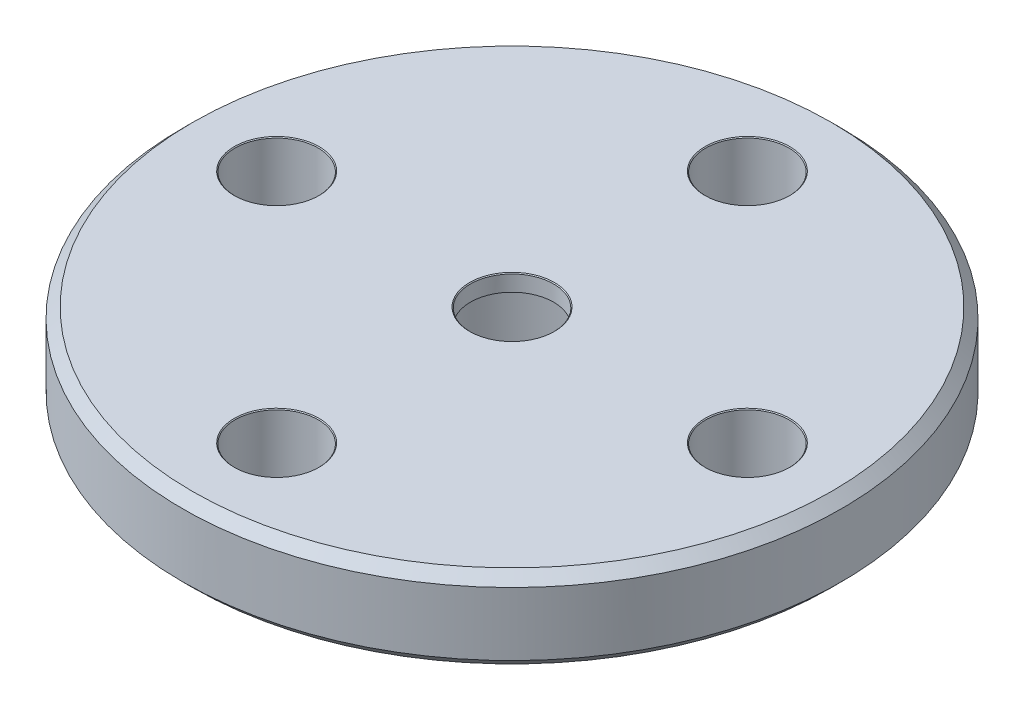
SolidWorks part; units mm, degrees
ref_plane "前视基准面" through (0, 0, 0) normal (0, 0, 1) x (1, 0, 0)
ref_plane "上视基准面" through (0, 0, 0) normal (0, 1, 0) x (1, 0, 0)
ref_plane "右视基准面" through (0, 0, 0) normal (1, 0, 0) x (0, 0, -1)
other "Configuration Table"
sketch "草图2" plane through (0, 0, 0) normal (0, 0, 1) x (1, 0, 0)
  line L0 (0, 0) -> (0, 4.6)
  line L1 (0, 4.6) -> (9.9, 4.6)
  line L2 (9.9, 4.6) -> (9.9, 2.1)
  line L3 (9.9, 2.1) -> (4.95, 2.1)
  line L4 (4.95, 2.1) -> (4.95, 0)
  line L5 (4.95, 0) -> (0, 0)
  dimension "D1" = 9.9
  dimension "D2" = 2.1
  dimension "D3" = 2.5
  dimension "D4" = 4.95
revolve "旋转1" add sketch "草图2" angle 360 about L0
chamfer "倒角1" distance 0.3 angle 45 3 edges at (0, 0, -4.95) (0, 2.1, -9.9) (0, 4.6, -9.9)
sketch "草图3" plane through (0, 4.6, 0) normal (0, 1, 0) x (1, 0, 0)
  line L0 (0, 0) -> (14.3811, 0) construction
  point P0 (7.0711, 0)
  point P4 (0, -7.0711)
  point P5 (-7.0711, 0)
  point P6 (0, 7.0711)
  point P7 (0, 0)
  dimension "D2" = 10
  dimension "D1" = 4
hole_wizard "M3 螺纹孔的螺纹孔钻头1" positions "草图3" profile "草图4" hole size "M3" standard "GB" end condition through all
sketch "草图4" plane through (7.0711, 4.6, 0) normal (1, 0, 0) x (0, 0, 1)
  line L0 (0, 0) -> (0, 4.6)
  line L1 (0, 4.6) -> (1.25, 4.6)
  line L2 (1.25, 4.6) -> (1.25, 0.025)
  line L3 (1.25, 0.025) -> (1.275, 0)
  line L5 (1.275, 0) -> (0, 0)
  line L6 (-1.25, 0.025) -> (-1.275, 0) construction
  line L11 (0, -6.35) -> (0, 107.95) construction
  dimension "通孔孔直径" = 2.5
  dimension "通孔孔深度" = 4.6
  dimension "近端锥形沉头孔直径" = 2.55
  dimension "近端锥形沉头孔角度" = 90
cosmetic thread "装饰螺纹线1"
cosmetic thread "装饰螺纹线2"
cosmetic thread "装饰螺纹线3"
cosmetic thread "装饰螺纹线4"
cosmetic thread "装饰螺纹线5"
sketch "草图5" plane through (0, 0, 0) normal (0, -1, 0) x (-1, 0, 0)
  circle A0 centre (0, 0) radius 2.75
  dimension "D1" = 5.5
extrude "切除-拉伸1" cut sketch "草图5" against normal offset from surface 0.5 and the other way through all contours A0 up to face at (7.0711, 4.6, 1.275)
